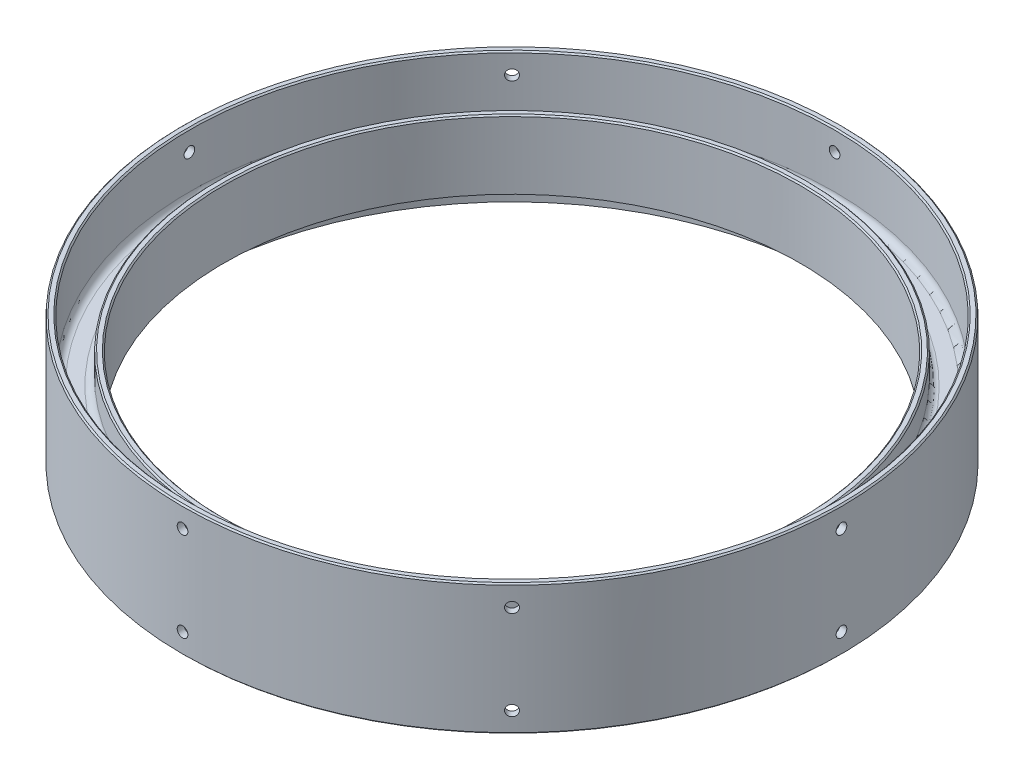
SolidWorks part; units mm, degrees
material "6061-T6 (SS)"
ref_plane "Front Plane" through (0, 0, 0) normal (0, 0, 1) x (1, 0, 0)
ref_plane "Top Plane" through (0, 0, 0) normal (0, 1, 0) x (1, 0, 0)
ref_plane "Right Plane" through (0, 0, 0) normal (1, 0, 0) x (0, 0, -1)
sketch "Sketch1" plane through (0, 0, 0) normal (0, 0, 1) x (1, 0, 0)
  line L0 (133.35, 15.875) -> (133.35, -15.875)
  line L1 (133.35, -15.875) -> (136.525, -15.875)
  line L2 (136.525, -15.875) -> (136.525, -1.5875)
  line L3 (136.525, -1.5875) -> (149.225, -1.5875)
  line L4 (149.225, -1.5875) -> (149.225, -30.1625)
  line L5 (149.225, -30.1625) -> (152.4, -30.1625)
  line L6 (152.4, -30.1625) -> (152.4, 30.1625)
  line L7 (152.4, 30.1625) -> (149.225, 30.1625)
  line L8 (149.225, 30.1625) -> (149.225, 1.5875)
  line L9 (149.225, 1.5875) -> (136.525, 1.5875)
  line L10 (136.525, 1.5875) -> (136.525, 15.875)
  line L11 (136.525, 15.875) -> (133.35, 15.875)
  line L12 (0, 0) -> (136.525, 0) construction
  line L13 (0, 44.4664) -> (0, -44.4664) construction
  point P17 (133.35, 0)
  dimension "D1" = 60.325
  dimension "D2" = 3.175
  dimension "D3" = 3.175
  dimension "D4" = 12.7
  dimension "D5" = 31.75
  dimension "D6" = 136.525
  dimension "D7" = 3.175
revolve "Revolve1" add sketch "Sketch1" angle 360 about L13
fillet "Fillet1" radius 3.175 4 edges at (0, -1.5875, 136.525) (0, -1.5875, 149.225) (0, 1.5875, 149.225) (0, 1.5875, 136.525)
sketch "Sketch3" plane through (0, 0, 0) normal (0, 1, 0) x (1, 0, 0)
  line L0 (88.9, 12.7) -> (88.9, -12.7)
  line L1 (88.9, -12.7) -> (131.9823, -19.05)
  line L2 (88.9, 12.7) -> (131.9823, 19.05)
  line L3 (0, 0) -> (88.9, 0) construction
  circle A0 centre (0, 0) radius 133.35 construction
  arc A1 (131.9823, -19.05) -> (131.9823, 19.05) centre (0, 0) ccw
  dimension "D1" = 88.9
  dimension "D2" = 25.4
  dimension "D3" = 38.1
ref_plane "Plane1" through (152.4, 0, 0) normal (1, 0, 0) x (0, 0, -1)
hole_wizard "#10 (0.1935) Diameter Hole1" positions "Sketch8" profile "Sketch9" hole size "#10" standard "ANSI Inch"
sketch "Sketch8" plane through (152.4, 0, 0) normal (1, 0, 0) x (0, 0, -1)
  line L0 (0, 20.6375) -> (0, -20.6375)
  point P0 (0, 20.6375)
  point P3 (0, -20.6375)
  point P9 (0, 0)
  dimension "D1" = 41.275
sketch "Sketch9" plane through (152.4, 20.6375, 0) normal (0, 1, 0) x (0, 0, -1)
  line L0 (0, 0) -> (0, 26.8766)
  line L1 (0, 26.8766) -> (2.4574, 25.4)
  line L2 (2.4574, 25.4) -> (2.4574, 0)
  line L5 (2.4574, 0) -> (0, 0)
  line L10 (0, 26.8766) -> (-2.4575, 25.4) construction
  line L11 (0, -6.35) -> (0, 107.95) construction
  dimension "Hole Dia." = 4.9149
  dimension "Hole Depth" = 25.4
  dimension "Drill Angle" = 118
pattern_circular "CirPattern7" count 8 over 360 about axis through (0, 30.1625, 0) along (0, 1, 0) of "#10 (0.1935) Diameter Hole1"
chamfer "Chamfer1" distance 0.635 angle 45 5 edges at (0, -30.1625, 152.4) (0, 30.1625, 152.4) (0, 30.1625, 149.225) (0, 15.875, 133.35) (0, 15.875, 136.525)
